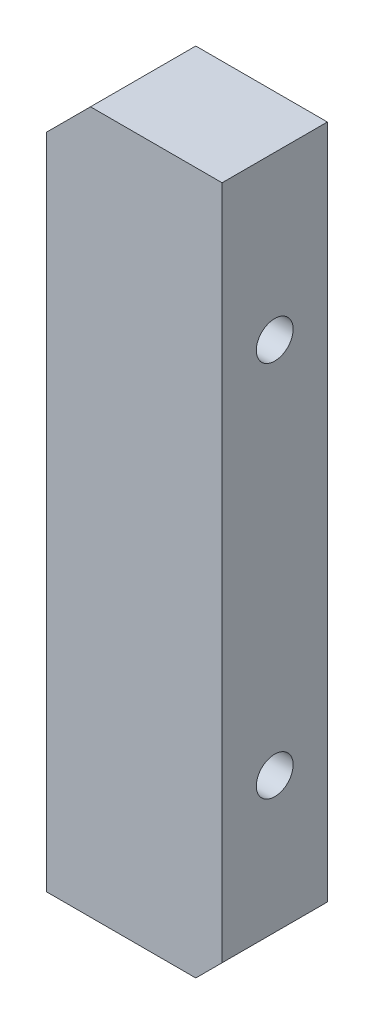
SolidWorks part; units mm, degrees
ref_plane "Front" through (0, 0, 0) normal (0, 0, 1) x (1, 0, 0)
ref_plane "Top" through (0, 0, 0) normal (0, 1, 0) x (1, 0, 0)
ref_plane "Right" through (0, 0, 0) normal (1, 0, 0) x (0, 0, -1)
sketch "Sketch1" plane through (0, 0, 0) normal (0, 0, 1) x (1, 0, 0)
  line L0 (0, 75) -> (5, 80)
  line L1 (0, 0) -> (17, 0)
  line L2 (0, 0) -> (0, 75)
  line L3 (5, 80) -> (20, 80)
  line L4 (20, 3) -> (20, 80)
  line L5 (17, 0) -> (20, 3)
  dimension "D1" = 20
  dimension "D2" = 80
  dimension "D3" = 17
  dimension "D4" = 5
  dimension "D5" = 75
  dimension "D6" = 3
extrude "Boss-Extrude1" add sketch "Sketch1" along normal blind 12
hole_wizard "M5x0.8 Tapped Hole1" positions "Sketch3" profile "Sketch2" tap size "M5x0.8" standard "JIS"
sketch "Sketch3" plane through (0, 0, 0) normal (0, -1, 0) x (1, 0, 0)
  line L0 (0, 0) -> (17, 0) construction
  line L1 (0, 12) -> (0, 0) construction
  point P0 (8, 6)
  dimension "D1" = 6
  dimension "D2" = 8
sketch "Sketch2" plane through (8, 0, 6) normal (1, 0, 0) x (0, 0, -1)
  line L0 (0, 0) -> (0, 15.2618)
  line L1 (0, 15.2618) -> (2.1, 14)
  line L2 (2.1, 14) -> (2.1, 0)
  line L5 (2.1, 0) -> (0, 0)
  line L10 (0, 15.2618) -> (-2.1, 14) construction
  line L11 (0, -6.35) -> (0, 107.95) construction
  dimension "ねじ下穴ﾄﾞﾘﾙ直径" = 4.2
  dimension "ねじ下穴ﾄﾞﾘﾙの深さ" = 14
  dimension "ﾄﾞﾘﾙ角度" = 118
cosmetic thread "Hole Thread1"
hole_wizard "M5x0.8 Tapped Hole2" positions "Sketch5" profile "Sketch4" tap size "M5x0.8" standard "JIS"
sketch "Sketch5" plane through (20, 0, 0) normal (1, 0, 0) x (0, 0, -1)
  line L0 (0, 3) -> (0, 80) construction
  line L1 (-12, 0) -> (0, 0) construction
  point P0 (-6, 18.5)
  point P6 (-6, 61.5)
  dimension "D1" = 6
  dimension "D2" = 18.5
  dimension "D3" = 43
sketch "Sketch4" plane through (20, 18.5, 6) normal (0, 1, 0) x (0, 0, -1)
  line L0 (0, 0) -> (0, 15.2618)
  line L1 (0, 15.2618) -> (2.1, 14)
  line L2 (2.1, 14) -> (2.1, 0)
  line L5 (2.1, 0) -> (0, 0)
  line L10 (0, 15.2618) -> (-2.1, 14) construction
  line L11 (0, -6.35) -> (0, 107.95) construction
  dimension "ねじ下穴ﾄﾞﾘﾙ直径" = 4.2
  dimension "ねじ下穴ﾄﾞﾘﾙの深さ" = 14
  dimension "ﾄﾞﾘﾙ角度" = 118
cosmetic thread "Hole Thread2"
cosmetic thread "Hole Thread3"
